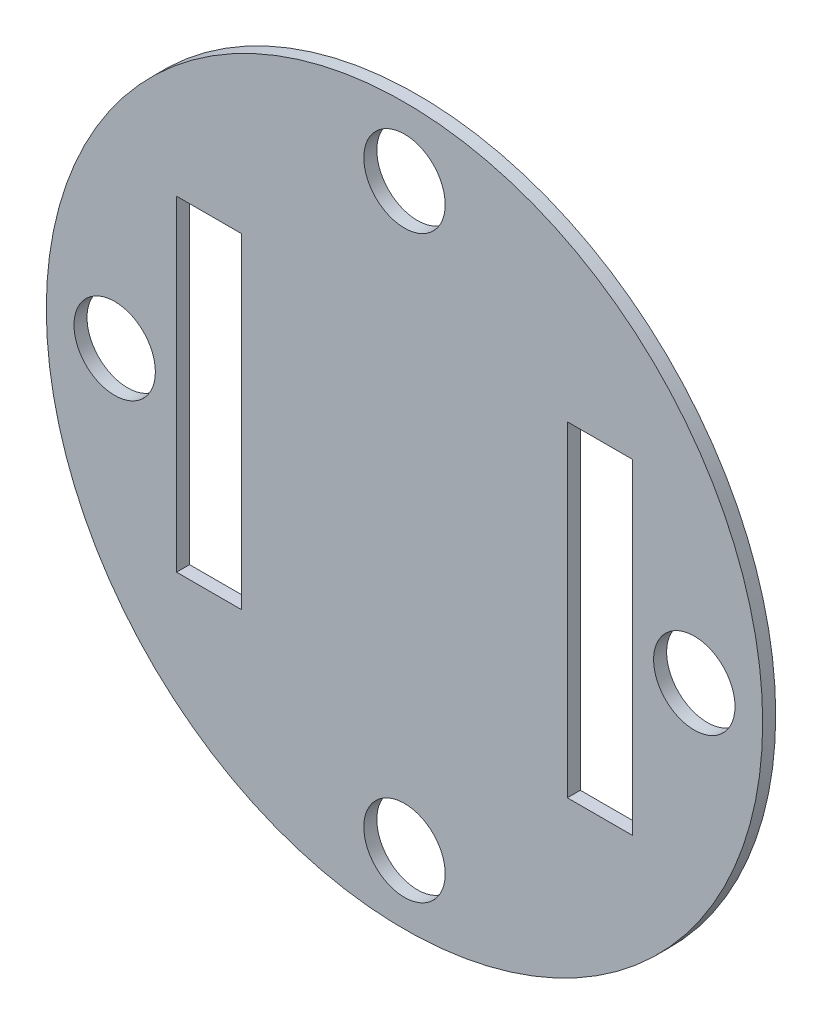
SolidWorks part; units mm, degrees
ref_plane "Front Plane" through (0, 0, 0) normal (0, 0, 1) x (1, 0, 0)
ref_plane "Top Plane" through (0, 0, 0) normal (0, 1, 0) x (1, 0, 0)
ref_plane "Right Plane" through (0, 0, 0) normal (1, 0, 0) x (0, 0, -1)
sketch "Sketch4" plane through (0, 0, 0) normal (0, 0, 1) x (1, 0, 0)
  circle A0 centre (0, 0) radius 59
  dimension "D1" = 118
extrude "Boss-Extrude3" add sketch "Sketch4" along normal blind 2
sketch "Sketch5" plane through (0, 0, 2) normal (0, 0, 1) x (1, 0, 0)
  line L1 (-22.5, 27.5) -> (22.5, 27.5)
  line L2 (-22.5, 27.5) -> (-22.5, -27.5)
  line L3 (-22.5, -27.5) -> (22.5, -27.5)
  line L4 (22.5, 27.5) -> (22.5, -27.5)
  circle A0 centre (0, 0) radius 59 construction
  circle A1 centre (-22.5, 27.5) radius 1.375
  circle A2 centre (22.5, 27.5) radius 1.375
  circle A3 centre (22.5, -27.5) radius 1.375
  circle A4 centre (-22.5, -27.5) radius 1.375
  dimension "D5" = 2.75
  dimension "D6" = 2.75
  dimension "D7" = 2.75
  dimension "D8" = 2.75
  dimension "D1" = 45
  dimension "D2" = 55
  dimension "D3" = 27.5
  dimension "D4" = 22.5
extrude "Boss-Extrude5" add sketch "Sketch5" along normal blind 7 contours A4 | A3 | A2 | A1
sketch "Sketch8" plane through (0, 0, 2) normal (0, 0, 1) x (1, 0, 0)
  circle A4 centre (-22.5, 27.5) radius 2.375
  circle A5 centre (-22.5, 27.5) radius 2.375
  circle A7 centre (22.5, 27.5) radius 2.375
  circle A8 centre (22.5, 27.5) radius 2.375
  circle A10 centre (-22.5, -27.5) radius 2.375
  circle A11 centre (-22.5, -27.5) radius 2.375
  circle A13 centre (22.5, -27.5) radius 2.375
  circle A14 centre (22.5, -27.5) radius 2.375
  dimension "D1" = 1
  dimension "D2" = 1
  dimension "D3" = 1
  dimension "D4" = 1
extrude "Boss-Extrude6" add sketch "Sketch8" along normal blind 2
sketch "Sketch9" plane through (0, 0, 2) normal (0, 0, 1) x (1, 0, 0)
  line L0 (4.7458, 55.7985) -> (5, 58.7878)
  line L1 (55.7985, -4.7458) -> (58.7878, -5)
  line L2 (-4.7458, 55.7985) -> (-5, 58.7878)
  line L3 (55.7985, 4.7458) -> (58.7878, 5)
  line L4 (-4.7458, -55.7985) -> (-5, -58.7878)
  line L5 (4.7458, -55.7985) -> (5, -58.7878)
  line L6 (-55.7985, 4.7458) -> (-58.7878, 5)
  line L7 (-55.7985, -4.7458) -> (-58.7878, -5)
  arc A0 (5, 58.7878) -> (-5, 58.7878) centre (0, 0) ccw
  arc A1 (5, 58.7878) -> (-5, 58.7878) centre (0, 0) ccw
  arc A2 (4.7458, 55.7985) -> (-4.7458, 55.7985) centre (0, 0) ccw
  arc A3 (55.7985, -4.7458) -> (55.7985, 4.7458) centre (0, 0) ccw
  arc A4 (58.7878, -5) -> (58.7878, 5) centre (0, 0) ccw
  arc A5 (-4.7458, -55.7985) -> (4.7458, -55.7985) centre (0, 0) ccw
  arc A6 (-5, -58.7878) -> (5, -58.7878) centre (0, 0) ccw
  arc A7 (-55.7985, 4.7458) -> (-55.7985, -4.7458) centre (0, 0) ccw
  arc A8 (-58.7878, 5) -> (-58.7878, -5) centre (0, 0) ccw
  point P25 (0, 0)
  circle M7 centre (0, 0) radius 59
  dimension "D1" = 118
  dimension "D2" = 3
  dimension "D3" = 4
extrude "Boss-Extrude7" add sketch "Sketch9" along normal blind 18 contours A2 L0 L2 M7 | A7 L6 L7 M7 | A4 L3 A3 L1 | A5 L5 A6 L4
sketch "Sketch10" plane through (0, 0, 2) normal (0, 0, 1) x (1, 0, 0)
  circle A0 centre (-40, 0) radius 7.5
  dimension "D1" = 15
  dimension "D2" = 40
extrude "Cut-Extrude1" cut sketch "Sketch10" against normal blind 18 contours A0
sketch "Sketch12" plane through (0, 0, 20) normal (0, 0, 1) x (1, 0, 0)
  circle A0 centre (0, 0) radius 57.5
  arc A1 (4.7458, 55.7985) -> (-4.7458, 55.7985) centre (0, 0) ccw construction
  dimension "D1" = 1.5
extrude "Cut-Extrude2" cut sketch "Sketch12" against normal blind 5
sketch "Sketch13" plane through (0, 0, 0) normal (0, 0, -1) x (-1, 0, 0)
  line L0 (-58.6183, 6.9928) -> (-53.5993, 6.5659)
  line L1 (-53.5993, -6.5659) -> (-58.6183, -6.9928)
  line L2 (6.9928, 58.6183) -> (6.5659, 53.5993)
  line L3 (-6.5659, 53.5993) -> (-6.9928, 58.6183)
  line L4 (58.6183, -6.9928) -> (53.5993, -6.5659)
  line L5 (53.5993, 6.5659) -> (58.6183, 6.9928)
  line L6 (-6.9928, -58.6183) -> (-6.5659, -53.5993)
  line L7 (6.5659, -53.5993) -> (6.9928, -58.6183)
  line L8 (5, 58.7878) -> (4.7458, 55.7985) construction
  line L9 (-4.7458, 55.7985) -> (-5, 58.7878) construction
  line L10 (55.7985, 4.7458) -> (58.7878, 5) construction
  line L11 (58.7878, -5) -> (55.7985, -4.7458) construction
  line L12 (4.7458, -55.7985) -> (5, -58.7878) construction
  line L13 (-5, -58.7878) -> (-4.7458, -55.7985) construction
  line L14 (-55.7985, -4.7458) -> (-58.7878, -5) construction
  line L15 (-58.7878, 5) -> (-55.7985, 4.7458) construction
  line L16 (4.7458, -55.7985) -> (5, -58.7878)
  line L17 (-5, -58.7878) -> (-4.7458, -55.7985)
  line L18 (-55.7985, -4.7458) -> (-58.7878, -5)
  line L19 (-58.7878, 5) -> (-55.7985, 4.7458)
  line L20 (-4.7458, 55.7985) -> (-5, 58.7878)
  line L21 (5, 58.7878) -> (4.7458, 55.7985)
  line L22 (55.7985, 4.7458) -> (58.7878, 5)
  line L23 (58.7878, -5) -> (55.7985, -4.7458)
  line L24 (4.8686, -57.2433) -> (5, -58.7878)
  line L25 (-5, -58.7878) -> (-4.8686, -57.2433)
  line L26 (-57.2433, -4.8686) -> (-58.7878, -5)
  line L27 (-58.7878, 5) -> (-57.2433, 4.8686)
  line L28 (-4.8686, 57.2433) -> (-5, 58.7878)
  line L29 (5, 58.7878) -> (4.8686, 57.2433)
  line L30 (57.2433, 4.8686) -> (58.7878, 5)
  line L31 (58.7878, -5) -> (57.2433, -4.8686)
  arc A0 (4.8686, 57.2433) -> (-4.8686, 57.2433) centre (0, 0) ccw
  circle A1 centre (0, 0) radius 59
  arc A2 (58.7878, -5) -> (58.7878, 5) centre (0, 0) ccw
  arc A3 (57.2433, -4.8686) -> (57.2433, 4.8686) centre (0, 0) ccw
  arc A4 (-4.8686, -57.2433) -> (4.8686, -57.2433) centre (0, 0) ccw
  arc A5 (-53.5993, 6.5659) -> (-53.5993, -6.5659) centre (0, 0) ccw
  arc A6 (6.5659, 53.5993) -> (-6.5659, 53.5993) centre (0, 0) ccw
  arc A7 (53.5993, -6.5659) -> (53.5993, 6.5659) centre (0, 0) ccw
  arc A8 (-6.5659, -53.5993) -> (6.5659, -53.5993) centre (0, 0) ccw
  circle A9 centre (0, 0) radius 59
  arc A10 (-5, -58.7878) -> (5, -58.7878) centre (0, 0) ccw
  arc A11 (-58.7878, 5) -> (-58.7878, -5) centre (0, 0) ccw
  arc A13 (-57.2433, 4.8686) -> (-57.2433, -4.8686) centre (0, 0) ccw
  arc A18 (5, -58.7878) -> (58.7878, -5) centre (0, 0) ccw
  arc A19 (-4.7458, -55.7985) -> (4.7458, -55.7985) centre (0, 0) ccw
  arc A20 (-58.7878, -5) -> (-5, -58.7878) centre (0, 0) ccw
  arc A21 (-55.7985, 4.7458) -> (-55.7985, -4.7458) centre (0, 0) ccw
  arc A22 (-5, 58.7878) -> (-58.7878, 5) centre (0, 0) ccw
  arc A23 (4.7458, 55.7985) -> (-4.7458, 55.7985) centre (0, 0) ccw
  arc A24 (58.7878, 5) -> (5, 58.7878) centre (0, 0) ccw
  arc A25 (55.7985, -4.7458) -> (55.7985, 4.7458) centre (0, 0) ccw
  arc A34 (4.7458, 55.7985) -> (-4.7458, 55.7985) centre (0, 0) ccw construction
  arc A35 (55.7985, -4.7458) -> (55.7985, 4.7458) centre (0, 0) ccw construction
  arc A36 (-4.7458, -55.7985) -> (4.7458, -55.7985) centre (0, 0) ccw construction
  arc A37 (-55.7985, 4.7458) -> (-55.7985, -4.7458) centre (0, 0) ccw construction
  dimension "D1" = 0
  dimension "D2" = 0
  dimension "D4" = 2
  dimension "D5" = 2
extrude "Cut-Extrude3" cut sketch "Sketch13" against normal blind 5.5
sketch "Sketch15" plane through (0, 0, 0) normal (0, 0, -1) x (-1, 0, 0)
  circle A0 centre (0, 0) radius 57
  circle A1 centre (0, 0) radius 89.714
  dimension "D1" = 114
extrude "Cut-Extrude4" cut sketch "Sketch15" against normal blind 22
sketch "Sketch16" plane through (0, 0, 2) normal (0, 0, 1) x (1, 0, 0)
  line L8 (55.7985, 4.7458) -> (56.7949, 4.8305)
  line L9 (4.8305, 56.7949) -> (4.7458, 55.7985)
  line L10 (-4.7458, 55.7985) -> (-4.8305, 56.7949)
  line L11 (-56.7949, 4.8305) -> (-55.7985, 4.7458)
  line L12 (-55.7985, -4.7458) -> (-56.7949, -4.8305)
  line L13 (-4.8305, -56.7949) -> (-4.7458, -55.7985)
  line L14 (4.7458, -55.7985) -> (4.8305, -56.7949)
  line L15 (56.7949, -4.8305) -> (55.7985, -4.7458)
  line L16 (55.7985, 4.7458) -> (56.7949, 4.8305)
  line L17 (4.8305, 56.7949) -> (4.7458, 55.7985)
  line L18 (-4.7458, 55.7985) -> (-4.8305, 56.7949)
  line L19 (-56.7949, 4.8305) -> (-55.7985, 4.7458)
  line L20 (-55.7985, -4.7458) -> (-56.7949, -4.8305)
  line L21 (-4.8305, -56.7949) -> (-4.7458, -55.7985)
  line L22 (4.7458, -55.7985) -> (4.8305, -56.7949)
  line L23 (56.7949, -4.8305) -> (55.7985, -4.7458)
  circle A0 centre (0, 0) radius 62.462
  arc A8 (56.7949, 4.8305) -> (4.8305, 56.7949) centre (0, 0) ccw
  arc A9 (4.7458, 55.7985) -> (-4.7458, 55.7985) centre (0, 0) ccw
  arc A10 (-4.8305, 56.7949) -> (-56.7949, 4.8305) centre (0, 0) ccw
  arc A11 (-55.7985, 4.7458) -> (-55.7985, -4.7458) centre (0, 0) ccw
  arc A12 (-56.7949, -4.8305) -> (-4.8305, -56.7949) centre (0, 0) ccw
  arc A13 (-4.7458, -55.7985) -> (4.7458, -55.7985) centre (0, 0) ccw
  arc A14 (4.8305, -56.7949) -> (56.7949, -4.8305) centre (0, 0) ccw
  arc A15 (55.7985, -4.7458) -> (55.7985, 4.7458) centre (0, 0) ccw
  arc A16 (56.7949, 4.8305) -> (4.8305, 56.7949) centre (0, 0) ccw
  arc A17 (4.7458, 55.7985) -> (-4.7458, 55.7985) centre (0, 0) ccw
  arc A18 (-4.8305, 56.7949) -> (-56.7949, 4.8305) centre (0, 0) ccw
  arc A19 (-55.7985, 4.7458) -> (-55.7985, -4.7458) centre (0, 0) ccw
  arc A20 (-56.7949, -4.8305) -> (-4.8305, -56.7949) centre (0, 0) ccw
  arc A21 (-4.7458, -55.7985) -> (4.7458, -55.7985) centre (0, 0) ccw
  arc A22 (4.8305, -56.7949) -> (56.7949, -4.8305) centre (0, 0) ccw
  arc A23 (55.7985, -4.7458) -> (55.7985, 4.7458) centre (0, 0) ccw
  dimension "D1" = 0
extrude "Cut-Extrude8" cut sketch "Sketch16" along normal blind 52 contours A0 | L16 A16 L17 A17 L18 A18 L19 A19 L20 A20 L21 A21 L22 A22 L23 A23
sketch "Sketch17" plane through (0, 0, 2) normal (0, 0, 1) x (1, 0, 0)
  line L0 (-5, 57) -> (5, 57)
  line L1 (5, 57) -> (4.8061, 54.7896)
  line L2 (-4.8061, 54.7896) -> (-5, 57)
  line L3 (54.7896, 4.8061) -> (57, 5)
  line L4 (57, 5) -> (57, -5)
  line L5 (57, -5) -> (54.7896, -4.8061)
  line L6 (4.8061, -54.7896) -> (5, -57)
  line L7 (5, -57) -> (-5, -57)
  line L8 (-5, -57) -> (-4.8061, -54.7896)
  line L9 (-54.7896, -4.8061) -> (-57, -5)
  line L10 (-57, -5) -> (-57, 5)
  line L11 (-57, 5) -> (-54.7896, 4.8061)
  arc A0 (4.8061, 54.7896) -> (-4.8061, 54.7896) centre (0, 0) ccw
  circle A1 centre (0, 0) radius 57 construction
  arc A2 (54.7896, -4.8061) -> (54.7896, 4.8061) centre (0, 0) ccw
  arc A3 (-4.8061, -54.7896) -> (4.8061, -54.7896) centre (0, 0) ccw
  arc A4 (-54.7896, 4.8061) -> (-54.7896, -4.8061) centre (0, 0) ccw
  point P8 (0, 57)
  point P24 (0, 0)
  dimension "D1" = 2
  dimension "D2" = 10
  dimension "D3" = 0
  dimension "D4" = 4
extrude "Cut-Extrude9" cut sketch "Sketch17" against normal blind 52
sketch "Sketch18" plane through (0, 0, 2) normal (0, 0, 1) x (1, 0, 0)
  circle A0 centre (0, 0) radius 55
  circle A1 centre (0, 0) radius 80.6225
  dimension "D1" = 110
extrude "Cut-Extrude10" cut sketch "Sketch18" against normal blind 10
sketch "Sketch19" plane through (0, 0, 2) normal (0, 0, 1) x (1, 0, 0)
  circle A0 centre (0, 0) radius 55
extrude "Boss-Extrude8" add sketch "Sketch19" against normal blind 2
sketch "Sketch20" plane through (0, 0, 2) normal (0, 0, 1) x (1, 0, 0)
  line L0 (0, 55) -> (0, -55) construction
  line L1 (-55, 0) -> (55, 0) construction
  circle A0 centre (0, 0) radius 55 construction
  circle A1 centre (0, 0) radius 44.5
  circle A2 centre (0, 44.5) radius 6.25
  circle A3 centre (44.5, 0) radius 6.25
  circle A4 centre (0, -44.5) radius 6.25
  circle A5 centre (-44.5, 0) radius 6.25
  dimension "D1" = 10.5
  dimension "D2" = 12.5
  dimension "D3" = 12.5
  dimension "D4" = 12.5
  dimension "D5" = 12.5
extrude "Cut-Extrude11" cut sketch "Sketch20" against normal blind 2 contours A3 | A2 | A5 | A4
sketch "Sketch21" plane through (0, 0, 2) normal (0, 0, 1) x (1, 0, 0)
  line L1 (25, 25) -> (35, 25)
  line L2 (25, 25) -> (25, -25)
  line L3 (25, -25) -> (35, -25)
  line L4 (35, 25) -> (35, -25)
  line L5 (-35, 25) -> (-25, 25)
  line L6 (-35, 25) -> (-35, -25)
  line L7 (-35, -25) -> (-25, -25)
  line L8 (-25, 25) -> (-25, -25)
  circle A0 centre (0, 0) radius 55 construction
  dimension "D5" = 25
  dimension "D1" = 10
  dimension "D2" = 10
  dimension "D3" = 50
  dimension "D4" = 50
  dimension "D6" = 25
  dimension "D7" = 25
  dimension "D8" = 25
extrude "Cut-Extrude12" cut sketch "Sketch21" against normal blind 3
sketch "Sketch22" plane through (0, 0, 2) normal (0, 0, 1) x (1, 0, 0)
  circle A0 centre (0, 0) radius 40.3946
extrude "Cut-Extrude13" cut sketch "Sketch22" along normal blind 10
